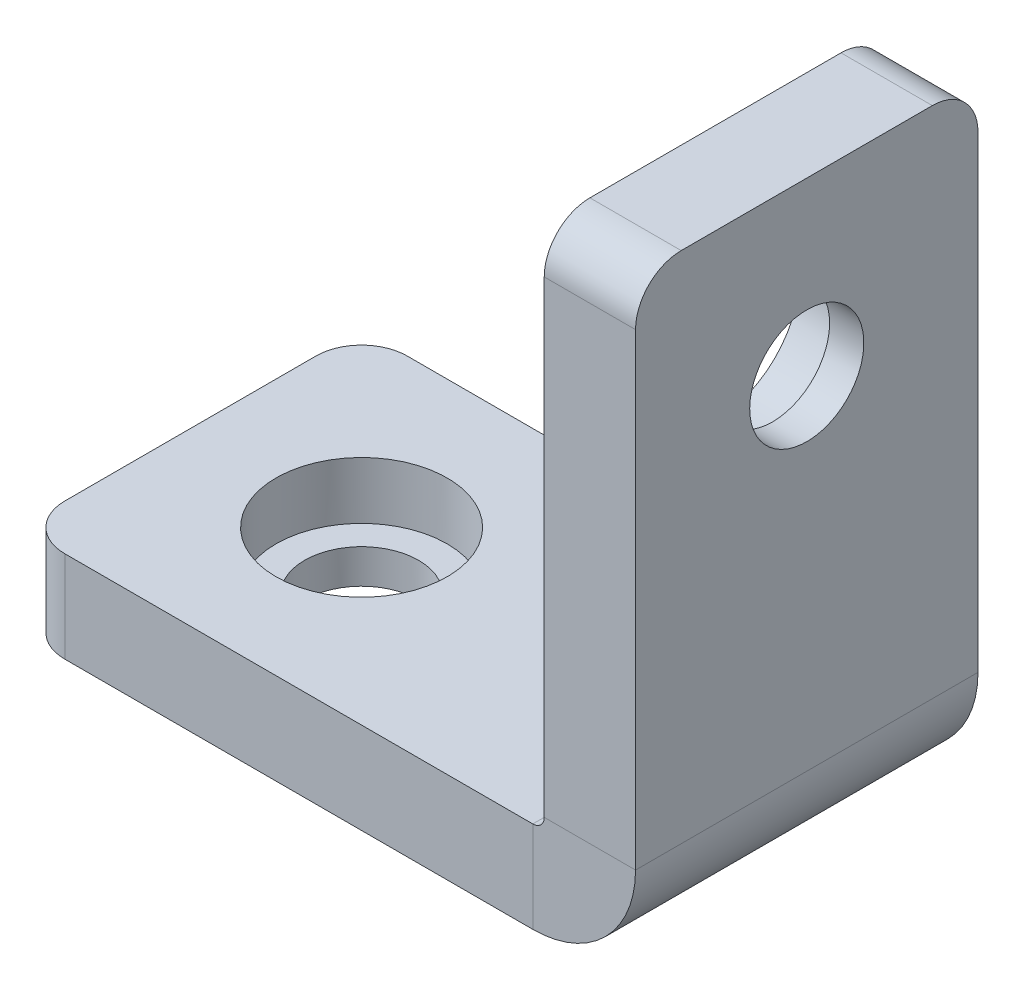
SolidWorks part; units mm, degrees
ref_plane "Front Plane" through (0, 0, 0) normal (0, 0, 1) x (1, 0, 0)
ref_plane "Top Plane" through (0, 0, 0) normal (0, 1, 0) x (1, 0, 0)
ref_plane "Right Plane" through (0, 0, 0) normal (1, 0, 0) x (0, 0, -1)
sketch "Sketch2" plane through (0, 0, 0) normal (0, 0, 1) x (1, 0, 0)
  line L0 (-2.5, 0) -> (-25, 0)
  line L1 (0, 2.5) -> (0, 25)
  arc A0 (-2.5, 0) -> (0, 2.5) centre (-2.5, 2.5) ccw
  point P6 (0, 0)
  dimension "D3" = 2.5
  dimension "D1" = 25
  dimension "D2" = 25
ref_plane "Plane1" through (-25, 0, 0) normal (1, 0, 0) x (0, 0, -1)
sketch "Sketch5" plane through (-25, 0, 0) normal (1, 0, 0) x (0, 0, -1)
  line L1 (-7.5, -2) -> (7.5, -2)
  line L2 (-7.5, -2) -> (-7.5, 2)
  line L3 (-7.5, 2) -> (7.5, 2)
  line L4 (7.5, -2) -> (7.5, 2)
  line L5 (-7.5, -2) -> (7.5, 2) construction
  line L6 (-7.5, 2) -> (7.5, -2) construction
  point P0 (0, 0)
  dimension "D1" = 15
  dimension "D2" = 4
sweep "Sweep1" add profiles "Sketch5" path "Sketch2"
sketch "Sketch6" plane through (0, 2, 0) normal (0, 1, 0) x (1, 0, 0)
  line L5 (-25, 7.5) -> (-2.5, 7.5) construction
  line L6 (-2.5, 7.5) -> (-25, 7.5) construction
  line L7 (-25, -15.9954) -> (-25, 15.9954) construction
  line L8 (-2.5, 7.5) -> (-2.5, -7.5) construction
  circle A0 centre (-17.5, 0) radius 2.5
  point P4 (-20, 0)
  point P5 (-17.5, 2.5)
  dimension "D1" = 5
  dimension "D2" = 22.5
  dimension "D3" = 15
sketch "Sketch7" plane through (-2, 0, 0) normal (-1, 0, 0) x (0, 0, 1)
  line L1 (-7.5, 25) -> (-7.5, 2.5) construction
  line L2 (-7.5, 2.5) -> (7.5, 2.5) construction
  circle A0 centre (0, 17.5) radius 2.5
  dimension "D1" = 5
  dimension "D2" = 22.5
  dimension "D3" = 15
extrude "Cut-Extrude2" cut sketch "Sketch7" against normal through all
fillet "Fillet1" radius 2 4 edges at (0, 25, -7.5) (0, 25, 7.5) (-25, 0, -7.5) (-25, 0, 7.5)
sketch "Sketch9" plane through (-2, 0, 0) normal (-1, 0, 0) x (0, 0, 1)
  circle A0 centre (0, 17.5) radius 3.7
  dimension "D1" = 7.4
extrude "Cut-Extrude3" cut sketch "Sketch9" against normal offset from surface (2.5 mm away) 1.5 up to face at (2, 17.5, 2.5)
extrude "Cut-Extrude4" cut sketch "Sketch6" against normal through all
sketch "Sketch10" plane through (0, 2, 0) normal (0, 1, 0) x (1, 0, 0)
  circle A0 centre (-17.5, 0) radius 3.75
  dimension "D1" = 7.5
extrude "Cut-Extrude5" cut sketch "Sketch10" against normal offset from surface (2.5 mm away) 1.5 up to face at (-17.5, -2, 2.5)
equation "\"D2@Sketch2\"=\"D1@Sketch2\""
equation "\"D3@Sketch7\"=\"D2@Sketch7\"*2/3"
equation "\"D3@Sketch6\"=\"D2@Sketch6\"*2/3"
